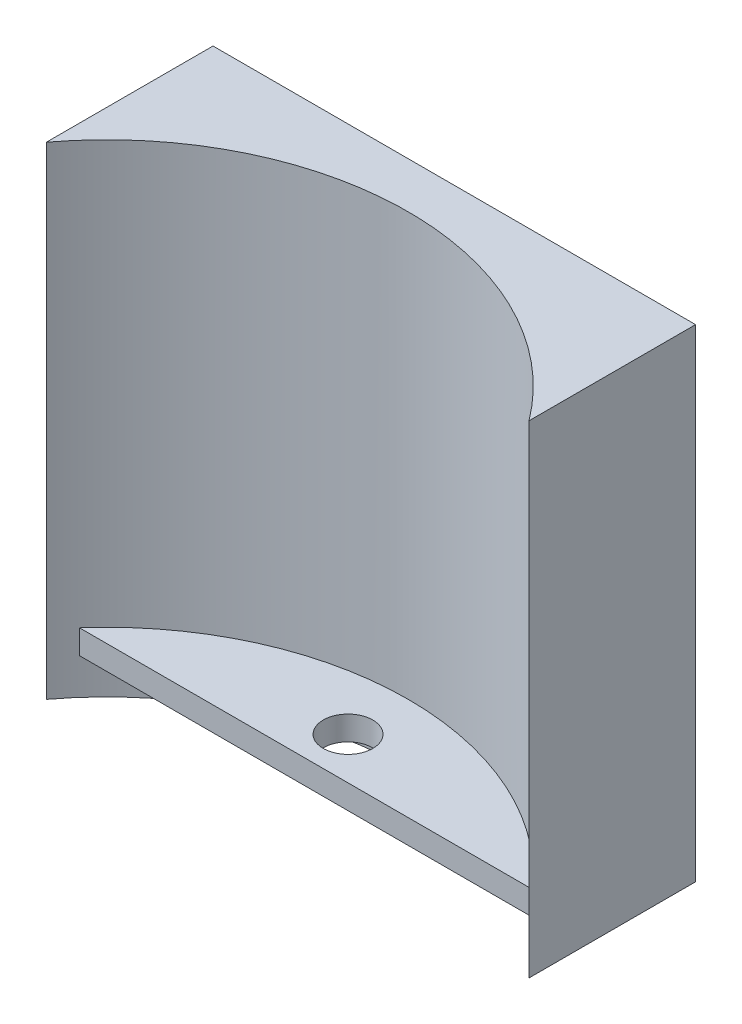
SolidWorks part; units mm, degrees
material "PTFE (general)"
ref_plane "Front Plane" through (0, 0, 0) normal (0, 0, 1) x (1, 0, 0)
ref_plane "Top Plane" through (0, 0, 0) normal (0, 1, 0) x (1, 0, 0)
ref_plane "Right Plane" through (0, 0, 0) normal (1, 0, 0) x (0, 0, -1)
sketch "Sketch6" plane through (0, 0, 0) normal (0, 1, 0) x (1, 0, 0)
  line L1 (20, 28.809) -> (-20, 28.809)
  line L2 (20, 28.809) -> (20, 15)
  line L4 (-20, 28.809) -> (-20, 15)
  circle A0 centre (0, 0) radius 25 construction
  arc A1 (20, 15) -> (-20, 15) centre (0, 0) ccw
  dimension "D1" = 50
  dimension "D2" = 40
  dimension "D3" = 20
extrude "Boss-Extrude1" add sketch "Sketch6" along normal blind 40
ref_plane "Plane1" through (0, 5, 0) normal (0, -1, 0) x (-1, 0, 0)
sketch "Sketch7" plane through (0, 5, 0) normal (0, -1, 0) x (-1, 0, 0)
  line L1 (20, 16.5089) -> (-20, 16.5089)
  line L2 (20, 16.5089) -> (20, 26.5089)
  line L3 (20, 26.5089) -> (-20, 26.5089)
  line L4 (-20, 16.5089) -> (-20, 26.5089)
  dimension "D1" = 40
  dimension "D2" = 20
  dimension "D3" = 10
extrude "Boss-Extrude2" add sketch "Sketch7" along normal blind 2
sketch "Sketch8" plane through (0, 3, 0) normal (0, -1, 0) x (1, 0, 0)
  line L0 (18.7739, -16.5089) -> (-18.7739, -16.5089) construction
  circle A0 centre (0, -20) radius 2.05
  circle A1 centre (0, 0) radius 20 construction
  point P4 (0, -16.5089)
  dimension "D1" = 4.1
  dimension "D3" = 40
  dimension "D2" = 0
extrude "Cut-Extrude1" cut sketch "Sketch8" against normal through all
equation "\"D3@Sketch6\"=\"D2@Sketch6\"/2"
